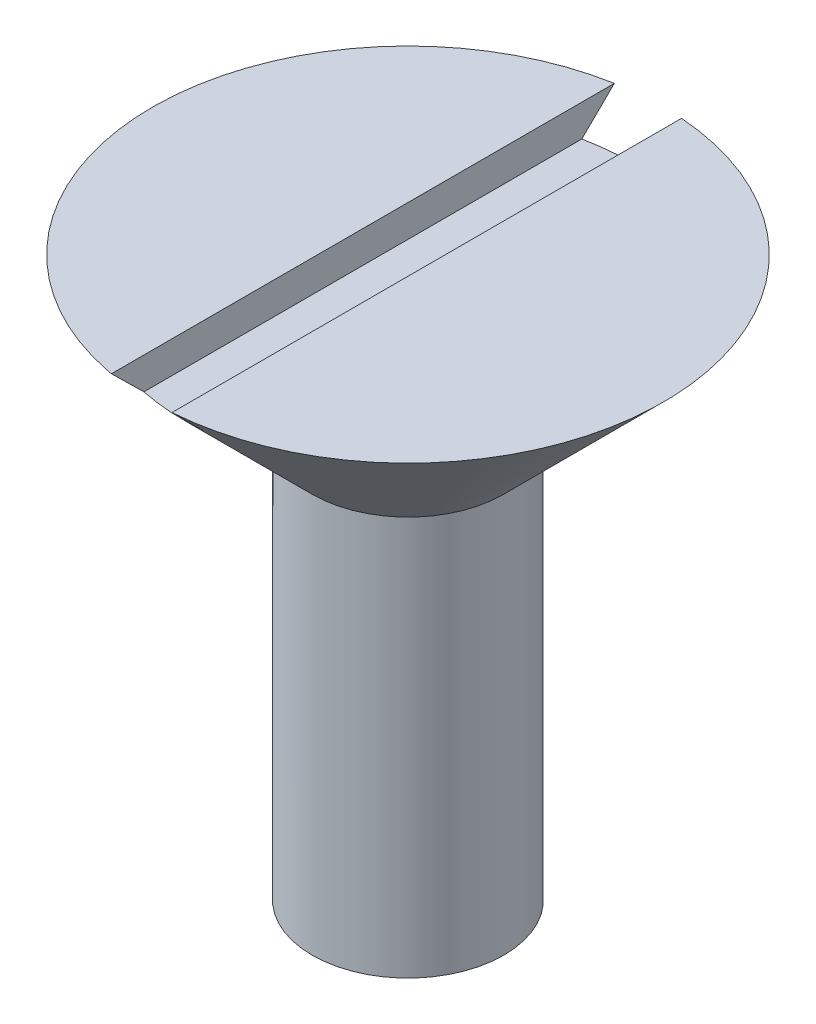
SolidWorks part; units mm, degrees
ref_plane "Front Plane" through (0, 0, 0) normal (0, 0, 1) x (1, 0, 0)
ref_plane "Top Plane" through (0, 0, 0) normal (0, 1, 0) x (1, 0, 0)
ref_plane "Right Plane" through (0, 0, 0) normal (1, 0, 0) x (0, 0, -1)
sketch "Sketch1" plane through (0, 0, 0) normal (0, 1, 0) x (1, 0, 0)
  circle A0 centre (0, 0) radius 3
  dimension "D1" = 6
extrude "Boss-Extrude1" add sketch "Sketch1" along normal blind 12.5
sketch "Sketch3" plane through (0, 0, 0) normal (0, 0, 1) x (1, 0, 0)
  line L0 (-3, 12.5) -> (-8, 17.5)
  line L1 (-8, 17.5) -> (0, 17.5)
  line L2 (0, 17.5) -> (0, 12.5)
  line L3 (3, 12.5) -> (-3, 12.5) construction
  line L4 (0, 12.5) -> (-3, 12.5)
  dimension "D1" = 45
  dimension "D2" = 5
revolve "Revolve1" add sketch "Sketch3" angle 360 about L2
sketch "Sketch4" plane through (0, 0, 0) normal (0, 0, 1) x (1, 0, 0)
  line L0 (0.5882, 17.501) -> (0.5882, 16.5)
  line L1 (0.5882, 16.5) -> (-1.4118, 16.5)
  line L2 (-1.4118, 16.5) -> (-1.4118, 17.501)
  line L3 (8, 17.5) -> (-8, 17.5) construction
  dimension "D1" = 2
  dimension "D2" = 1
extrude "Cut-Extrude4" cut sketch "Sketch4" against normal through all and the other way through all flip side to cut
sketch "Sketch6" plane through (0, 0, 0) normal (0, 0, 1) x (1, 0, 0)
  line L0 (3, 0) -> (0, -1.7321)
  line L1 (0, -1.7321) -> (0, 0) construction
  line L2 (0, 0) -> (3, 0)
  line L3 (0, -1.7321) -> (0, 0)
revolve "Revolve2" add sketch "Sketch6" angle 360 about L1
